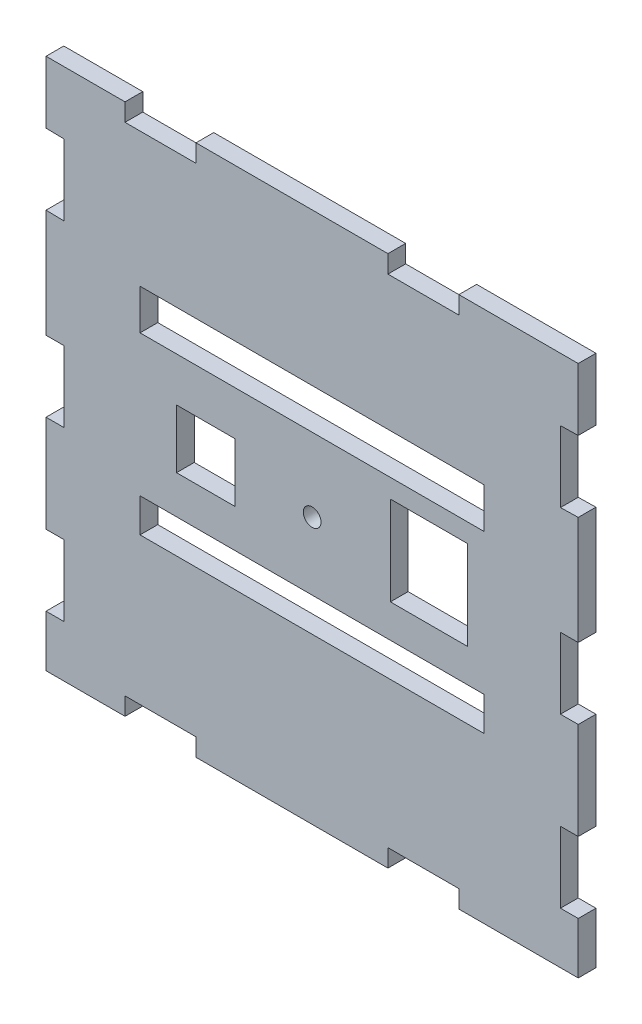
SolidWorks part; units mm, degrees
ref_plane "Front Plane" through (0, 0, 0) normal (0, 0, 1) x (1, 0, 0)
ref_plane "Top Plane" through (0, 0, 0) normal (0, 1, 0) x (1, 0, 0)
ref_plane "Right Plane" through (0, 0, 0) normal (1, 0, 0) x (0, 0, -1)
sketch "Sketch1" plane through (0, 0, 0) normal (0, 0, 1) x (1, 0, 0)
  line L1 (-75, -75) -> (-52.7387, -75)
  line L2 (-75, -75) -> (-75, -60.4642)
  line L3 (-75, 75) -> (-52.7387, 75)
  line L4 (75, -75) -> (75, -60.4642)
  line L5 (-75, -75) -> (75, 75) construction
  line L6 (-75, 75) -> (75, -75) construction
  line L7 (-52.7387, 75) -> (-52.7387, 70)
  line L8 (-32.7387, 75) -> (-32.7387, 70)
  line L9 (-52.7387, 70) -> (-32.7387, 70)
  line L11 (21.3609, 75) -> (21.3609, 70)
  line L12 (41.3609, 75) -> (41.3609, 70)
  line L13 (21.3609, 70) -> (41.3609, 70)
  line L15 (-75, 57.4357) -> (-70.001, 57.3354)
  line L16 (-75, 37.4357) -> (-70.001, 37.3354)
  line L17 (-70.001, 57.3354) -> (-70.001, 37.3354)
  line L19 (-75, 6.8909) -> (-70, 6.8909)
  line L20 (-75, -13.1091) -> (-70, -13.1091)
  line L21 (-70, 6.8909) -> (-70, -13.1091)
  line L22 (-75, -40.4642) -> (-70, -40.4642)
  line L24 (-70, -40.4642) -> (-70, -60.4642)
  line L25 (-75, -60.4642) -> (-70, -60.4642)
  line L26 (-70, 0) -> (70, 0) construction
  line L27 (0, 75) -> (0, -75) construction
  line L28 (41.3609, -75) -> (41.3609, -70)
  line L29 (21.3609, -75) -> (21.3609, -70)
  line L30 (21.3609, -70) -> (41.3609, -70)
  line L31 (-32.7387, -75) -> (-32.7387, -70)
  line L32 (-52.7387, -75) -> (-52.7387, -70)
  line L33 (-52.7387, -70) -> (-32.7387, -70)
  line L34 (75, -60.4642) -> (70, -60.4642)
  line L35 (70, -40.4642) -> (70, -60.4642)
  line L36 (75, -40.4642) -> (70, -40.4642)
  line L37 (75, -13.1091) -> (70, -13.1091)
  line L38 (70, 6.8909) -> (70, -13.1091)
  line L39 (75, 6.8909) -> (70, 6.8909)
  line L40 (75, 37.4357) -> (70.001, 37.3354)
  line L41 (70.001, 57.3354) -> (70.001, 37.3354)
  line L42 (75, 57.4357) -> (70.001, 57.3354)
  line L43 (-32.7387, 75) -> (21.3609, 75)
  line L44 (41.3609, 75) -> (75, 75)
  line L45 (75, 57.4357) -> (75, 75)
  line L46 (75, 6.8909) -> (75, 37.4357)
  line L47 (75, -40.4642) -> (75, -13.1091)
  line L48 (41.3609, -75) -> (75, -75)
  line L49 (-32.7387, -75) -> (21.3609, -75)
  line L50 (-75, -40.4642) -> (-75, -13.1091)
  line L51 (-75, 6.8909) -> (-75, 37.4357)
  line L52 (-75, 57.4357) -> (-75, 75)
  line L54 (-48.5052, 32.111) -> (48.5052, 32.111)
  line L55 (-48.5052, 32.111) -> (-48.5052, 20.7299)
  line L56 (-48.5052, 20.7299) -> (48.5052, 20.7299)
  line L57 (48.5052, 32.111) -> (48.5052, 20.7299)
  line L58 (-48.5052, 32.111) -> (48.5052, 20.7299) construction
  line L59 (-48.5052, 20.7299) -> (48.5052, 32.111) construction
  line L60 (-48.5052, -19.0401) -> (48.5052, -19.0401)
  line L61 (-48.5052, -19.0401) -> (-48.5052, -28.5882)
  line L62 (-48.5052, -28.5882) -> (48.5052, -28.5882)
  line L63 (48.5052, -19.0401) -> (48.5052, -28.5882)
  line L64 (-48.5052, -19.0401) -> (48.5052, -28.5882) construction
  line L65 (-48.5052, -28.5882) -> (48.5052, -19.0401) construction
  line L66 (-38.2228, 8.2671) -> (-21.799, 8.2671)
  line L67 (-38.2228, 8.2671) -> (-38.2228, -8.2671)
  line L68 (-38.2228, -8.2671) -> (-21.799, -8.2671)
  line L69 (-21.799, 8.2671) -> (-21.799, -8.2671)
  line L70 (-38.2228, 8.2671) -> (-21.799, -8.2671) construction
  line L71 (-38.2228, -8.2671) -> (-21.799, 8.2671) construction
  line L72 (22.0496, 15.439) -> (43.7415, 15.439)
  line L73 (22.0496, 15.439) -> (22.0496, -9.6616)
  line L74 (22.0496, -9.6616) -> (43.7415, -9.6616)
  line L75 (43.7415, 15.439) -> (43.7415, -9.6616)
  line L76 (22.0496, 15.439) -> (43.7415, -9.6616) construction
  line L77 (22.0496, -9.6616) -> (43.7415, 15.439) construction
  circle A0 centre (0, 0) radius 2.5
  point P0 (0, 0)
  point P52 (0, 26.4204)
  point P57 (0, -23.8142)
  point P62 (-30.0109, 0)
  point P67 (32.8955, 2.8887)
  dimension "D13" = 5
  dimension "D1" = 150
  dimension "D2" = 150
  dimension "D3" = 20
  dimension "D4" = 5
  dimension "D5" = 5
  dimension "D6" = 20
  dimension "D7" = 5
  dimension "D8" = 5
  dimension "D9" = 5
  dimension "D10" = 20
  dimension "D11" = 20
  dimension "D12" = 20
  dimension "D14" = 5
  dimension "D15" = 5
extrude "Boss-Extrude1" add sketch "Sketch1" along normal blind 5
